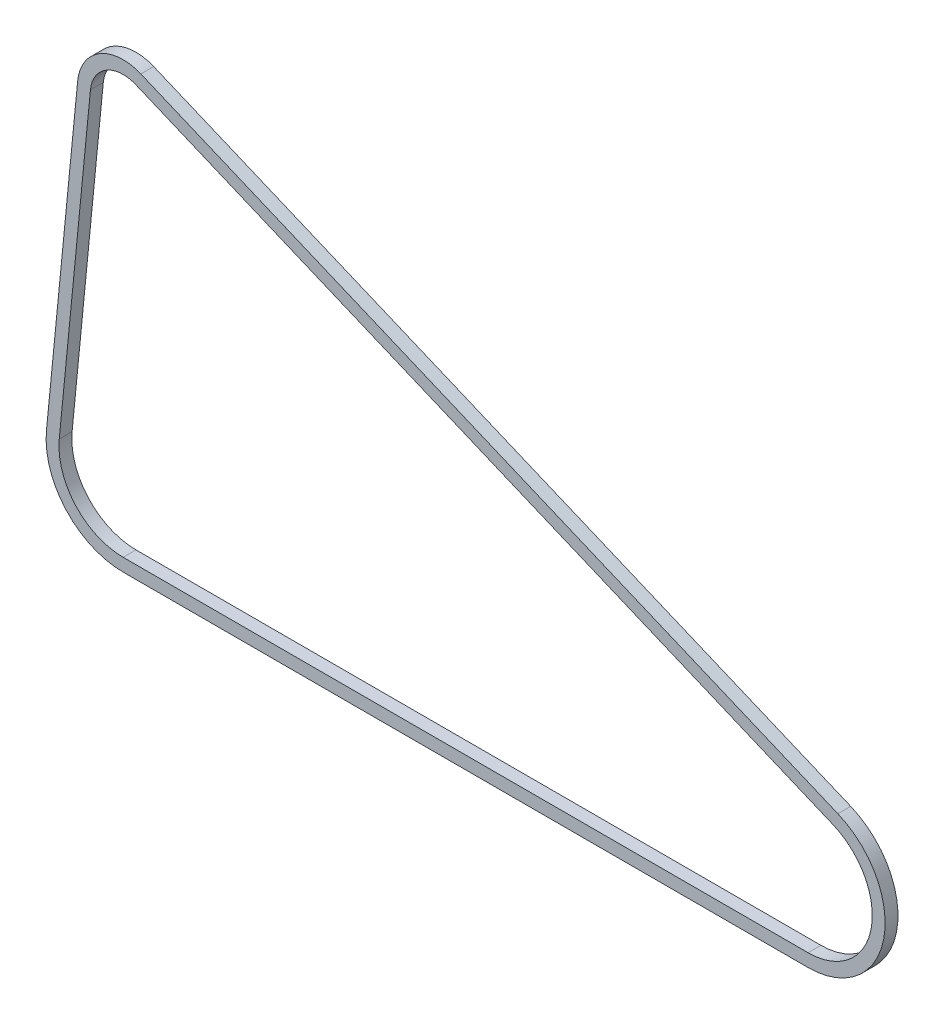
SolidWorks part; units mm, degrees
ref_plane "Front Plane" through (0, 0, 0) normal (0, 0, 1) x (1, 0, 0)
ref_plane "Top Plane" through (0, 0, 0) normal (0, 1, 0) x (1, 0, 0)
ref_plane "Right Plane" through (0, 0, 0) normal (1, 0, 0) x (0, 0, -1)
sketch "Sketch2" plane through (0, 0, 0) normal (0, 0, 1) x (1, 0, 0)
  line L0 (0, 0) -> (1, 0) construction
  line L1 (0, 0) -> (0, 1) construction
  line L2 (4.9091, 11.7128) -> (-132.9541, 69.4948)
  line L3 (-141.9356, 64.1346) -> (-148.106, 1.24)
  line L4 (-135.4667, -12.7) -> (0, -12.7)
  arc A0 (0, -12.7) -> (4.9091, 11.7128) centre (0, 0) ccw
  arc A1 (-132.9541, 69.4948) -> (-141.9356, 64.1346) centre (-135.4667, 63.5) ccw
  arc A2 (-148.106, 1.24) -> (-135.4667, -12.7) centre (-135.4667, 0) ccw
sketch "Sketch3" plane through (0, 0, 0) normal (0, 0, 1) x (1, 0, 0)
  line L3 (-141.9356, 64.1346) -> (-148.106, 1.24) construction
  line L4 (-135.4667, -12.7) -> (0, -12.7) construction
  line L5 (4.9091, 11.7128) -> (-132.9541, 69.4948) construction
  line L6 (5.891, 14.0554) -> (-131.9723, 71.8373)
  line L7 (-144.4635, 64.3826) -> (-150.6339, 1.488)
  line L8 (-135.4667, -15.24) -> (0, -15.24)
  line L9 (5.891, 14.0554) -> (-131.9723, 71.8373)
  line L10 (-144.4635, 64.3826) -> (-150.6339, 1.488)
  line L11 (-135.4667, -15.24) -> (0, -15.24)
  line L12 (-141.9356, 64.1346) -> (-148.106, 1.24)
  line L13 (-135.4667, -12.7) -> (0, -12.7)
  line L14 (4.9091, 11.7128) -> (-132.9541, 69.4948)
  arc A3 (-148.106, 1.24) -> (-135.4667, -12.7) centre (-135.4667, 0) ccw construction
  arc A4 (0, -12.7) -> (4.9091, 11.7128) centre (0, 0) ccw construction
  arc A5 (-132.9541, 69.4948) -> (-141.9356, 64.1346) centre (-135.4667, 63.5) ccw construction
  arc A6 (-131.9723, 71.8373) -> (-144.4635, 64.3826) centre (-135.4667, 63.5) ccw
  arc A7 (-150.6339, 1.488) -> (-135.4667, -15.24) centre (-135.4667, 0) ccw
  arc A8 (0, -15.24) -> (5.891, 14.0554) centre (0, 0) ccw
  arc A9 (-131.9723, 71.8373) -> (-144.4635, 64.3826) centre (-135.4667, 63.5) ccw
  arc A10 (-150.6339, 1.488) -> (-135.4667, -15.24) centre (-135.4667, 0) ccw
  arc A11 (0, -15.24) -> (5.891, 14.0554) centre (0, 0) ccw
  arc A12 (-148.106, 1.24) -> (-135.4667, -12.7) centre (-135.4667, 0) ccw
  arc A13 (0, -12.7) -> (4.9091, 11.7128) centre (0, 0) ccw
  arc A14 (-132.9541, 69.4948) -> (-141.9356, 64.1346) centre (-135.4667, 63.5) ccw
  dimension "D1" = 2.54
extrude "Boss-Extrude1" add sketch "Sketch3" along normal mid plane 2.54
